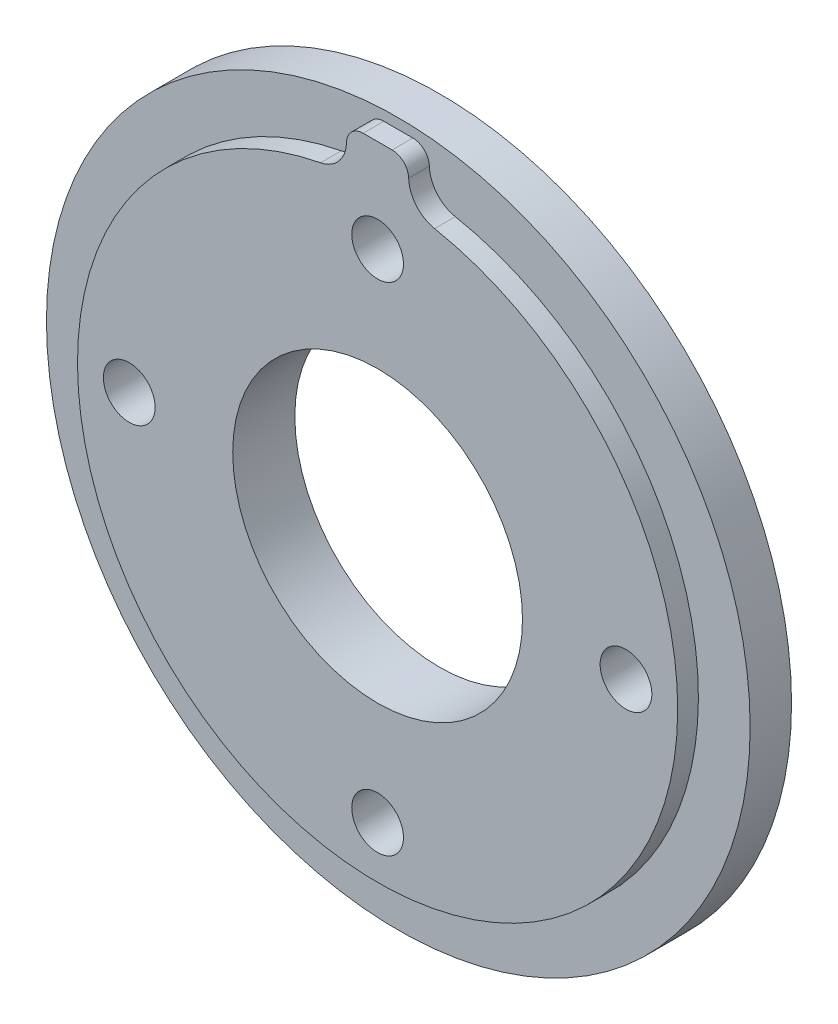
SolidWorks part; units mm, degrees
ref_plane "正面" through (0, 0, 0) normal (0, 0, 1) x (1, 0, 0)
ref_plane "平面" through (0, 0, 0) normal (0, 1, 0) x (1, 0, 0)
ref_plane "右側面" through (0, 0, 0) normal (1, 0, 0) x (0, 0, -1)
sketch "ｽｹｯﾁ1" plane through (0, 0, 0) normal (0, 0, 1) x (1, 0, 0)
  circle A0 centre (0, 0) radius 17
  dimension "D1" = 34
extrude "ﾎﾞｽ - 押し出し1" add sketch "ｽｹｯﾁ1" along normal blind 2
sketch "ｽｹｯﾁ2" plane through (0, 0, 2) normal (0, 0, 1) x (1, 0, 0)
  line L1 (-1.5, 12.5) -> (1.5, 12.5)
  line L2 (-1.5, 12.5) -> (-1.5, 16.5)
  line L3 (-1.5, 16.5) -> (1.5, 16.5)
  line L4 (1.5, 12.5) -> (1.5, 16.5)
  line L5 (-1.5, 12.5) -> (1.5, 16.5) construction
  line L6 (-1.5, 16.5) -> (1.5, 12.5) construction
  circle A0 centre (0, 0) radius 14.5
  point P3 (0, 14.5)
  circle M5 centre (0, 0) radius 17
  dimension "D1" = 29
  dimension "D2" = 2
  dimension "D3" = 3
extrude "ﾎﾞｽ - 押し出し2" add sketch "ｽｹｯﾁ2" along normal blind 1 contours A0 L4 L2 M5 | L4 L3 L2 M5 | L2 A0 L4 L1 | L4 A0 L2 L1
fillet "ﾌｨﾚｯﾄ1" radius 1.55 2 edges at (-1.5, 14.4222, 2.5) (1.5, 14.4222, 2.5)
fillet "ﾌｨﾚｯﾄ2" radius 0.8 2 edges at (1.5, 16.5, 2.5) (-1.5, 16.5, 2.5)
sketch "ｽｹｯﾁ3" plane through (0, 0, 3) normal (0, 0, 1) x (1, 0, 0)
  circle A0 centre (0, 0) radius 7
  dimension "D1" = 14
extrude "ｶｯﾄ - 押し出し1" cut sketch "ｽｹｯﾁ3" against normal through all
sketch "ｽｹｯﾁ4" plane through (0, 0, 0) normal (0, 0, -1) x (-1, 0, 0)
  circle A0 centre (0, 0) radius 12 construction
  circle A1 centre (0, 12) radius 1.25
  circle A2 centre (12, 0) radius 1.25
  circle A3 centre (0, -12) radius 1.25
  circle A4 centre (-12, 0) radius 1.25
  point P14 (0, 0)
  dimension "D1" = 24
  dimension "D2" = 2.5
  dimension "D3" = 4
extrude "ｶｯﾄ - 押し出し2" cut sketch "ｽｹｯﾁ4" against normal through all
